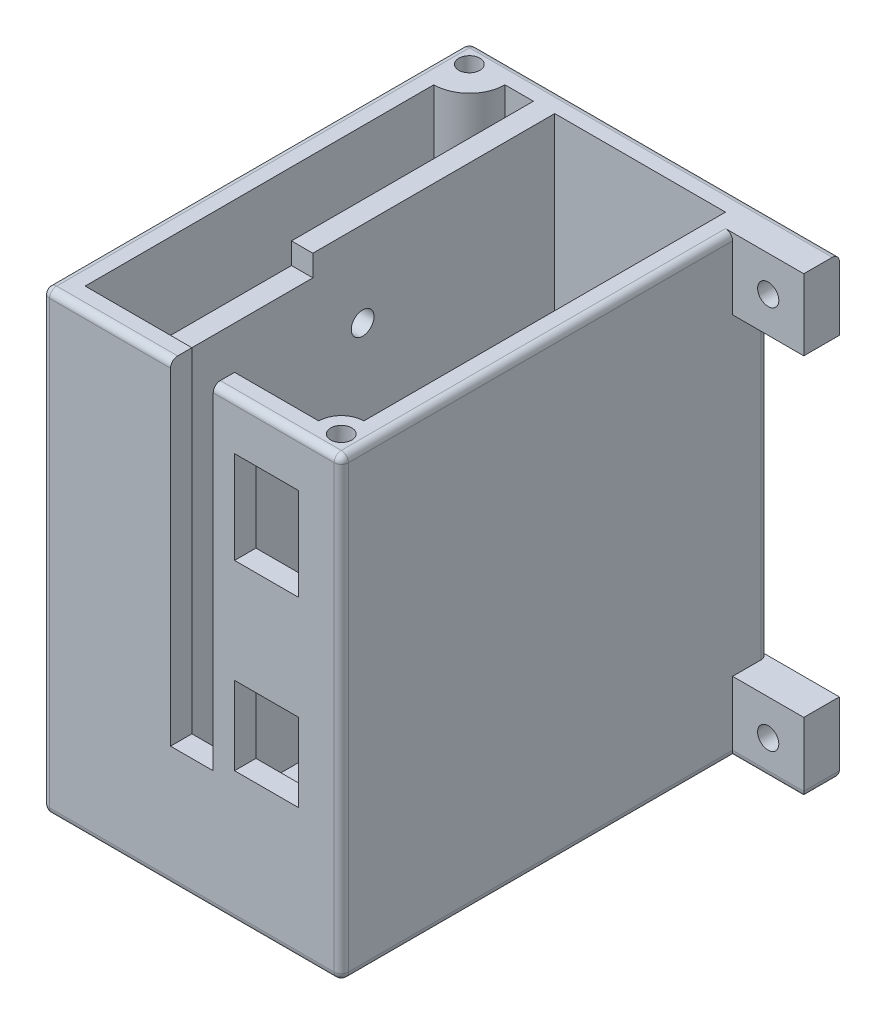
SolidWorks part; units mm, degrees
ref_plane "Front Plane" through (0, 0, 0) normal (0, 0, 1) x (1, 0, 0)
ref_plane "Top Plane" through (0, 0, 0) normal (0, 1, 0) x (1, 0, 0)
ref_plane "Right Plane" through (0, 0, 0) normal (1, 0, 0) x (0, 0, -1)
sketch "Sketch1" plane through (0, 0, 0) normal (0, 1, 0) x (1, 0, 0)
  line L1 (-549.0437, 369.3934) -> (-507.0437, 369.3934)
  line L2 (-549.0437, 369.3934) -> (-549.0437, 309.3934)
  line L3 (-549.0437, 309.3934) -> (-507.0437, 309.3934)
  line L4 (-507.0437, 369.3934) -> (-507.0437, 309.3934)
  dimension "D1" = 60
  dimension "D2" = 42
extrude "Boss-Extrude1" add sketch "Sketch1" along normal blind 64
sketch "Sketch2" plane through (0, 64, 0) normal (0, 1, 0) x (1, 0, 0)
  line L0 (-507.0437, 369.3934) -> (-549.0437, 369.3934) construction
  line L1 (-546.0437, 366.3934) -> (-510.0437, 366.3934)
  line L2 (-546.0437, 366.3934) -> (-546.0437, 312.3934)
  line L3 (-546.0437, 312.3934) -> (-510.0437, 312.3934)
  line L4 (-510.0437, 366.3934) -> (-510.0437, 312.3934)
  line L5 (-549.0437, 369.3934) -> (-549.0437, 309.3934) construction
  line L7 (-507.0437, 309.3934) -> (-507.0437, 369.3934) construction
  line L8 (-549.0437, 309.3934) -> (-507.0437, 309.3934) construction
  dimension "D1" = 3
  dimension "D2" = 3
  dimension "D3" = 3
  dimension "D4" = 3
  dimension "D5" = 3
  dimension "D6" = 3
extrude "Cut-Extrude1" cut sketch "Sketch2" against normal blind 61
sketch "Sketch5" plane through (0, 3, 0) normal (0, 1, 0) x (1, 0, 0)
  line L0 (-510.0437, 366.3934) -> (-546.0437, 366.3934) construction
  line L1 (-534.0437, 366.3934) -> (-537.0437, 366.3934)
  line L2 (-534.0437, 366.3934) -> (-534.0437, 312.3934)
  line L3 (-534.0437, 312.3934) -> (-537.0437, 312.3934)
  line L4 (-537.0437, 366.3934) -> (-537.0437, 312.3934)
  line L5 (-546.0437, 312.3934) -> (-510.0437, 312.3934) construction
  line L6 (-510.0437, 312.3934) -> (-510.0437, 366.3934) construction
  line L7 (-546.0437, 366.3934) -> (-546.0437, 312.3934) construction
  dimension "D1" = 3
  dimension "D2" = 0
  dimension "D3" = 0
  dimension "D4" = 24
  dimension "D5" = 9
extrude "Boss-Extrude2" add sketch "Sketch5" along normal blind 61
sketch "Sketch6" plane through (0, 0, -312.3934) normal (0, 0, -1) x (-1, 0, 0)
  line L0 (534.0437, 3) -> (510.0437, 3) construction
  line L1 (525.0437, 17) -> (531.0437, 17)
  line L2 (525.0437, 17) -> (525.0437, 64)
  line L3 (525.0437, 64) -> (531.0437, 64)
  line L4 (531.0437, 17) -> (531.0437, 64)
  line L5 (534.0437, 64) -> (534.0437, 3) construction
  line L6 (534.0437, 64) -> (510.0437, 64) construction
  point P8 (528.0437, 64)
  dimension "D1" = 14
  dimension "D2" = 3
  dimension "D3" = 6
  dimension "D4" = 0
extrude "Cut-Extrude3" cut sketch "Sketch6" against normal blind 3
sketch "Sketch7" plane through (0, 3, 0) normal (0, 1, 0) x (1, 0, 0)
  line L0 (-534.0437, 312.3934) -> (-534.0437, 366.3934) construction
  line L1 (-525.0437, 331.3934) -> (-531.0437, 331.3934)
  line L2 (-525.0437, 331.3934) -> (-525.0437, 315.3934)
  line L3 (-525.0437, 315.3934) -> (-531.0437, 315.3934)
  line L4 (-531.0437, 331.3934) -> (-531.0437, 315.3934)
  line L5 (-534.0437, 312.3934) -> (-510.0437, 312.3934) construction
  dimension "D1" = 6
  dimension "D2" = 3
  dimension "D3" = 3
  dimension "D4" = 16
extrude "Cut-Extrude4" cut sketch "Sketch7" against normal blind 3
sketch "Sketch9" plane through (0, 0, 0) normal (0, -1, 0) x (1, 0, 0)
  line L0 (-507.0437, -309.3934) -> (-507.0437, -369.3934) construction
  line L1 (-549.0437, -309.3934) -> (-507.0437, -309.3934) construction
  line L2 (-507.0437, -313.3934) -> (-507.0437, -309.3934)
  line L3 (-507.0437, -309.3934) -> (-511.0437, -309.3934)
  arc A0 (-511.0437, -309.3934) -> (-507.0437, -313.3934) centre (-510.0437, -312.3934) ccw
  dimension "D1" = 3
  dimension "D2" = 3
extrude "Boss-Extrude3" add sketch "Sketch9" against normal blind 64
sketch "Sketch10" plane through (0, 0, 0) normal (0, -1, 0) x (-1, 0, 0)
  line L0 (507.0437, 309.3934) -> (507.0437, 369.3934) construction
  line L1 (549.0437, 309.3934) -> (507.0437, 309.3934) construction
  circle A0 centre (510.0437, 312.3934) radius 1.48
  dimension "D1" = 3
  dimension "D2" = 3
extrude "Cut-Extrude6" cut sketch "Sketch10" against normal blind 64
sketch "Sketch11" plane through (0, 0, 0) normal (0, -1, 0) x (1, 0, 0)
  line L0 (-507.0437, -369.3934) -> (-549.0437, -369.3934) construction
  line L1 (-549.0437, -369.3934) -> (-549.0437, -309.3934) construction
  line L2 (-542.0437, -369.3934) -> (-549.0437, -369.3934)
  line L3 (-549.0437, -369.3934) -> (-549.0437, -362.3934)
  arc A0 (-542.0437, -369.3934) -> (-549.0437, -362.3934) centre (-546.0437, -366.3934) ccw
  dimension "D1" = 3
  dimension "D2" = 3
extrude "Boss-Extrude4" add sketch "Sketch11" against normal blind 64
sketch "Sketch12" plane through (0, 0, 0) normal (0, -1, 0) x (-1, 0, 0)
  line L0 (507.0437, 369.3934) -> (549.0437, 369.3934) construction
  line L1 (549.0437, 369.3934) -> (549.0437, 309.3934) construction
  circle A0 centre (546.0437, 366.3934) radius 1.48
  dimension "D1" = 3
  dimension "D2" = 3
extrude "Cut-Extrude7" cut sketch "Sketch12" against normal blind 64
sketch "Sketch13" plane through (-507.0437, 0, 0) normal (1, 0, 0) x (0, 0, -1)
  line L1 (369.3934, 64) -> (364.3934, 64)
  line L2 (369.3934, 64) -> (369.3934, 54)
  line L3 (369.3934, 54) -> (364.3934, 54)
  line L4 (364.3934, 64) -> (364.3934, 54)
  dimension "D1" = 5
  dimension "D2" = 10
extrude "Boss-Extrude5" add sketch "Sketch13" along normal blind 10
sketch "Sketch14" plane through (0, 0, -369.3934) normal (0, 0, -1) x (-1, 0, 0)
  line L0 (497.0437, 54) -> (497.0437, 64) construction
  line L1 (497.0437, 54) -> (507.0437, 54) construction
  circle A0 centre (502.0437, 59) radius 1.49
  dimension "D1" = 5
  dimension "D2" = 5
extrude "Cut-Extrude8" cut sketch "Sketch14" against normal blind 5
sketch "Sketch15" plane through (-507.0437, 0, 0) normal (1, 0, 0) x (0, 0, -1)
  line L1 (369.3934, 0) -> (364.3934, 0)
  line L2 (369.3934, 0) -> (369.3934, 10)
  line L3 (369.3934, 10) -> (364.3934, 10)
  line L4 (364.3934, 0) -> (364.3934, 10)
  dimension "D1" = 5
  dimension "D2" = 10
extrude "Boss-Extrude6" add sketch "Sketch15" along normal blind 10
sketch "Sketch16" plane through (0, 0, -364.3934) normal (0, 0, 1) x (1, 0, 0)
  line L0 (-497.0437, 10) -> (-497.0437, 0) construction
  line L1 (-497.0437, 0) -> (-507.0437, 0) construction
  circle A0 centre (-502.0437, 5) radius 1.49
  dimension "D1" = 5
  dimension "D2" = 5
extrude "Cut-Extrude9" cut sketch "Sketch16" against normal blind 5
sketch "Sketch17" plane through (-534.0437, 0, 0) normal (1, 0, 0) x (0, 0, -1)
  line L0 (312.3934, 64) -> (366.3934, 64) construction
  line L1 (366.3934, 64) -> (366.3934, 3) construction
  circle A0 centre (339.3934, 52) radius 1.6
  dimension "D1" = 12
  dimension "D2" = 27
extrude "Cut-Extrude10" cut sketch "Sketch17" against normal blind 3
fillet "Fillet1" radius 1 15 edges at (-507.0437, 0, -336.8934) (-502.0437, 0, -364.3934) (-497.0437, 0, -366.8934) (-549.0437, 0, -339.3934) (-528.0437, 0, -309.3934) (-523.0437, 64, -369.3934) (-549.0437, 64, -339.3934) (-549.0437, 32, -369.3934) (-549.0437, 32, -309.3934) (-540.0437, 64, -309.3934) (-516.0437, 64, -309.3934) (-507.0437, 32, -369.3934) (-507.0437, 64, -336.8934) (-507.0437, 32, -309.3934) (-523.0437, 0, -369.3934)
sketch "Sketch21" plane through (0, 0, -309.3934) normal (0, 0, 1) x (1, 0, 0)
  line L0 (-525.0437, 63) -> (-525.0437, 17) construction
  line L1 (-513.0437, 57.1066) -> (-522.0437, 57.1066)
  line L2 (-513.0437, 57.1066) -> (-513.0437, 44.1066)
  line L3 (-513.0437, 44.1066) -> (-522.0437, 44.1066)
  line L4 (-522.0437, 57.1066) -> (-522.0437, 44.1066)
  line L5 (-513.0437, 29.5116) -> (-522.0437, 29.5116)
  line L6 (-513.0437, 29.5116) -> (-513.0437, 18.5116)
  line L7 (-513.0437, 18.5116) -> (-522.0437, 18.5116)
  line L8 (-522.0437, 29.5116) -> (-522.0437, 18.5116)
  dimension "D1" = 9
  dimension "D2" = 13
  dimension "D3" = 3
  dimension "D4" = 9
  dimension "D5" = 11
  dimension "D6" = 3
extrude "Cut-Extrude11" cut sketch "Sketch21" against normal blind 3
sketch "Sketch23" plane through (-534.0437, 0, 0) normal (1, 0, 0) x (0, 0, -1)
  line L1 (312.3934, 64) -> (332.3934, 64)
  line L2 (312.3934, 64) -> (312.3934, 61)
  line L3 (312.3934, 61) -> (332.3934, 61)
  line L4 (332.3934, 64) -> (332.3934, 61)
  dimension "D1" = 3
  dimension "D2" = 20
extrude "Cut-Extrude12" cut sketch "Sketch23" against normal blind 3
